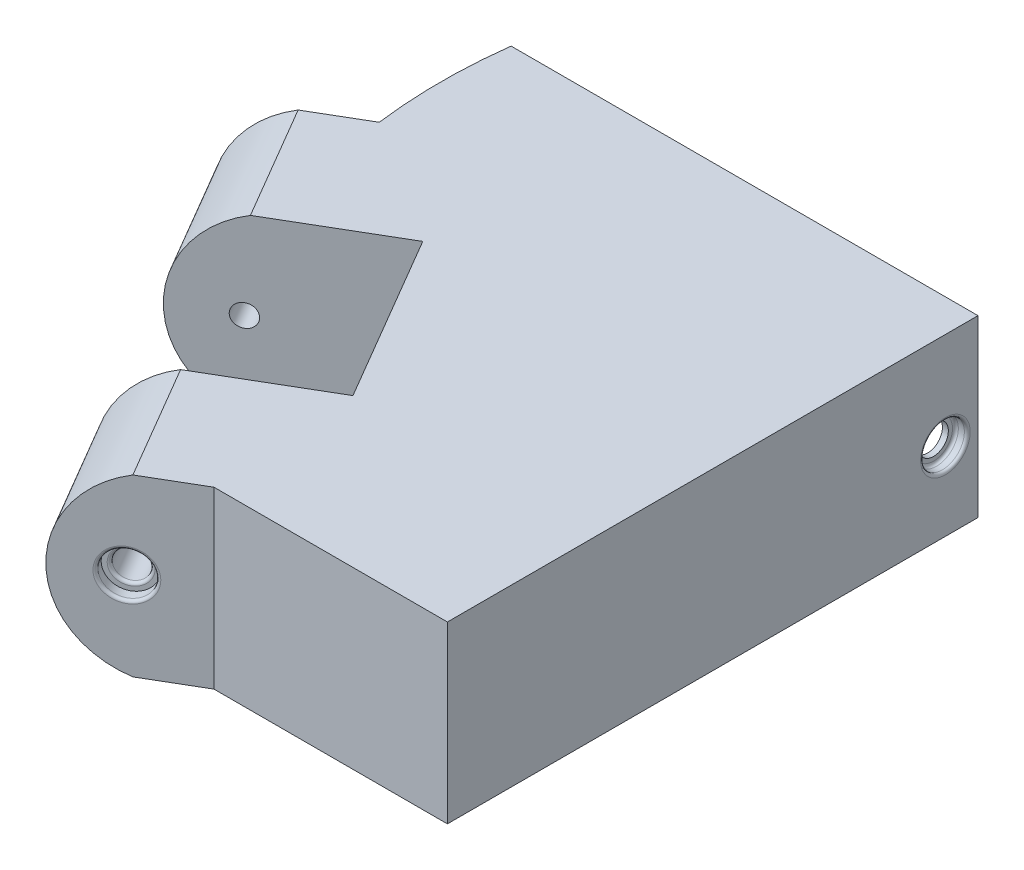
SolidWorks part; units mm, degrees
material "ABS PC"
ref_plane "Front Plane" through (0, 0, 0) normal (0, 0, 1) x (1, 0, 0)
ref_plane "Top Plane" through (0, 0, 0) normal (0, 1, 0) x (1, 0, 0)
ref_plane "Right Plane" through (0, 0, 0) normal (1, 0, 0) x (0, 0, -1)
sketch "Sketch1" plane through (0, 0, 0) normal (0, 1, 0) x (1, 0, 0)
  line L0 (-40.005, 22.86) -> (0, -45.466)
  line L1 (-40.005, -45.466) -> (40.005, -45.466)
  line L2 (-40.005, -45.466) -> (-40.005, 45.466)
  line L3 (-40.005, 45.466) -> (40.005, 45.466)
  line L4 (40.005, -45.466) -> (40.005, 45.466)
  line L5 (40.005, 45.466) -> (-40.005, -45.466) construction
  line L6 (40.005, -45.466) -> (0, 0) construction
  point P4 (-40.005, 22.86)
  point P5 (0.127, -45.466)
  dimension "D1" = 80.01
  dimension "D2" = 22.606
  dimension "D3" = 90.932
  dimension "D4" = 39.878
extrude "Boss-Extrude2" add sketch "Sketch1" along normal blind 29.972 contours L1 L4 L3 L2 L0
sketch "Sketch8" plane through (0, 0, 0) normal (0, 1, 0) x (1, 0, 0)
  line L0 (-40.005, 22.86) -> (0, -45.466) construction
  line L1 (-40.005, 22.86) -> (-28.4546, 3.1327)
  line L2 (-11.5504, -25.7387) -> (0, -45.466)
  line L3 (-40.005, 22.86) -> (0, -45.466) construction
  point P0 (-28.4546, 3.1327)
  point P1 (-11.5504, -25.7387)
  dimension "D1" = 22.86
  dimension "D2" = 22.86
extrude "Extrude-Thin2" add sketch "Sketch8" along normal blind 29.972 thin
ref_plane "Plane1" through (21.1078, 0, 36.0507) normal (0.5053, 0, 0.863) x (0.863, 0, -0.5053)
sketch "Sketch10" plane through (19.8244, 0, 33.8588) normal (0.5053, 0, 0.863) x (0.863, 0, -0.5053)
  line L0 (-22.9725, 0) -> (-33.1325, 0) construction
  line L1 (-33.1325, 29.972) -> (-33.1325, 0) construction
  line L2 (-33.1325, 29.972) -> (-33.1325, 0)
  arc A0 (-33.1325, 29.972) -> (-33.1325, 0) centre (-28.2931, 14.986) ccw
  dimension "D1" = 15.748
extrude "Boss-Extrude3" add sketch "Sketch10" against normal blind 22.86
sketch "Sketch11" plane through (-8.6302, 0, -14.7399) normal (0.5053, 0, 0.863) x (0.863, 0, -0.5053)
  line L0 (-33.1325, 0) -> (-33.1325, 29.972)
  arc A0 (-33.1325, 29.972) -> (-33.1325, 0) centre (-28.2931, 14.986) ccw
  dimension "D1" = 15.748
extrude "Boss-Extrude4" add sketch "Sketch11" against normal blind 22.86
sketch "Sketch12" plane through (21.1078, 0, 36.0507) normal (0.5053, 0, 0.863) x (0.863, 0, -0.5053)
  circle A0 centre (-33.8811, 14.986) radius 1.905
  arc A1 (-33.1325, 29.972) -> (-33.1325, 0) centre (-28.2931, 14.986) ccw construction
  point P2 (-44.0411, 14.986)
  dimension "D1" = 3.81
  dimension "D2" = 14.986
  dimension "D3" = 10.16
extrude "Cut-Extrude2" cut sketch "Sketch12" against normal through all contours A0
ref_plane "Plane2" through (8.274, 0, 14.1314) normal (0.5053, 0, 0.863) x (0.863, 0, -0.5053)
sketch "Sketch15" plane through (0, 29.972, 0) normal (0, 1, 0) x (1, 0, 0)
  line L0 (-40.005, 45.466) -> (-40.005, 22.86)
  arc A0 (-40.005, 22.86) -> (-40.005, 45.466) centre (48.2158, 34.163) cw
  dimension "D1" = 88.9419
extrude "Boss-Extrude6" add sketch "Sketch15" against normal blind 29.972
hole_wizard "CBORE for #6 Pan Head Machine Screw1" positions "Sketch17" profile "Sketch16" counterbore size "#6" standard "ANSI Inch" end condition through all
sketch "Sketch17" plane through (19.8244, 0, 33.8588) normal (0.5053, 0, 0.863) x (0.863, 0, -0.5053)
  point P0 (-33.8811, 14.986)
sketch "Sketch16" plane through (-9.4138, 14.986, 50.9778) normal (0, 1, 0) x (0.863, 0, -0.5053)
  line L0 (0, 0) -> (0, 107.8707)
  line L1 (0, 107.8707) -> (1.875, 107.8707)
  line L3 (1.875, 107.8707) -> (1.875, 2.032)
  line L4 (1.875, 2.032) -> (3.75, 2.032)
  line L5 (3.75, 2.032) -> (3.75, 0)
  line L7 (3.75, 0) -> (0, 0)
  line L11 (0, -6.35) -> (0, 107.95) construction
  dimension "Thru Hole Dia." = 3.75
  dimension "Thru Hole Depth" = 107.8707
  dimension "C'Bore Dia." = 7.5
  dimension "C'Bore Depth" = 2.032
sketch "Sketch18" plane through (18.7977, 0, 32.1052) normal (0.5053, 0, 0.863) x (0.863, 0, -0.5053)
  circle A0 centre (-33.8811, 14.986) radius 2.5
  circle A1 centre (-33.8811, 14.986) radius 1.905 construction
  dimension "D1" = 5
extrude "Cut-Extrude4" cut sketch "Sketch18" against normal up to surface (20.828 mm away)
fillet "Fillet1" radius 0.5 2 edges at (-6.1776, 14.986, 49.083) (-8.2831, 14.986, 47.9611)
sketch "Sketch19" plane through (0, 0, -45.466) normal (0, 0, -1) x (-1, 0, 0)
  line L1 (-36.957, 0) -> (37.0121, 0)
  line L2 (-36.957, 0) -> (-36.957, 25.4)
  line L3 (-36.957, 25.4) -> (37.0121, 25.4)
  line L4 (37.0121, 0) -> (37.0121, 25.4)
  line L5 (-36.957, 0) -> (37.0121, 25.4) construction
  line L6 (-36.957, 25.4) -> (37.0121, 0) construction
  line L9 (-40.005, 29.972) -> (-40.005, 0) construction
  point P0 (0.0276, 12.7)
  point P8 (0, 16.6255)
  dimension "D1" = 25.4
  dimension "D2" = 73.9691
  dimension "D3" = 12.7
  dimension "D4" = 3.048
extrude "Cut-Extrude5" cut sketch "Sketch19" against normal blind 22.86 contours L3 L4 L1 L2
sketch "Sketch21" plane through (40.005, 0, 0) normal (1, 0, 0) x (0, 0, -1)
  line L1 (45.466, 29.972) -> (45.466, 0) construction
  circle A0 centre (39.878, 13.3918) radius 1.905
  dimension "D1" = 3.81
  dimension "D2" = 5.588
  dimension "D3" = 42.0666
extrude "Cut-Extrude7" cut sketch "Sketch21" against normal up to surface (80.4041 mm away) contours A0
hole_wizard "CBORE for #6 Pan Head Machine Screw2" positions "Sketch25" profile "Sketch24" counterbore size "#6" standard "ANSI Inch" end condition through all
sketch "Sketch25" plane through (40.005, 0, 0) normal (1, 0, 0) x (0, 0, -1)
  point P0 (39.878, 13.3918)
sketch "Sketch24" plane through (40.005, 13.3918, -39.878) normal (0, 1, 0) x (0, 0, -1)
  line L0 (0, 0) -> (0, 98.1915)
  line L1 (0, 98.1915) -> (1.875, 98.1915)
  line L3 (1.875, 98.1915) -> (1.875, 2.032)
  line L4 (1.875, 2.032) -> (3.75, 2.032)
  line L5 (3.75, 2.032) -> (3.75, 0)
  line L7 (3.75, 0) -> (0, 0)
  line L11 (0, -6.35) -> (0, 107.95) construction
  dimension "Thru Hole Dia." = 3.75
  dimension "Thru Hole Depth" = 98.1915
  dimension "C'Bore Dia." = 7.5
  dimension "C'Bore Depth" = 2.032
sketch "Sketch26" plane through (40.005, 0, 0) normal (1, 0, 0) x (0, 0, -1)
  circle A0 centre (39.878, 13.3918) radius 2.54
  circle A1 centre (39.878, 13.3918) radius 1.905 construction
  dimension "D1" = 5.08
extrude "Cut-Extrude9" cut sketch "Sketch26" against normal up to surface (3.048 mm away) contours A0 up to face at (36.957, 13.3918, -37.973)
fillet "Fillet3" radius 0.5 2 edges at (40.005, 13.3918, -43.628) (37.973, 13.3918, -43.628)
sketch "Sketch28" plane through (0, 29.972, 0) normal (0, 1, 0) x (1, 0, 0)
  line L0 (-11.5504, -25.7387) -> (-1.6867, -19.9635)
  line L1 (-1.6867, -19.9635) -> (-18.5909, 8.9079)
  line L2 (-18.5909, 8.9079) -> (-28.4546, 3.1327)
  line L3 (-28.4546, 3.1327) -> (-11.5504, -25.7387)
  dimension "D1" = 11.43
  dimension "D2" = 11.43
extrude "Cut-Extrude11" cut sketch "Sketch28" against normal up to surface (29.972 mm away) up to face at (-10.6657, 0, -5.8436)
